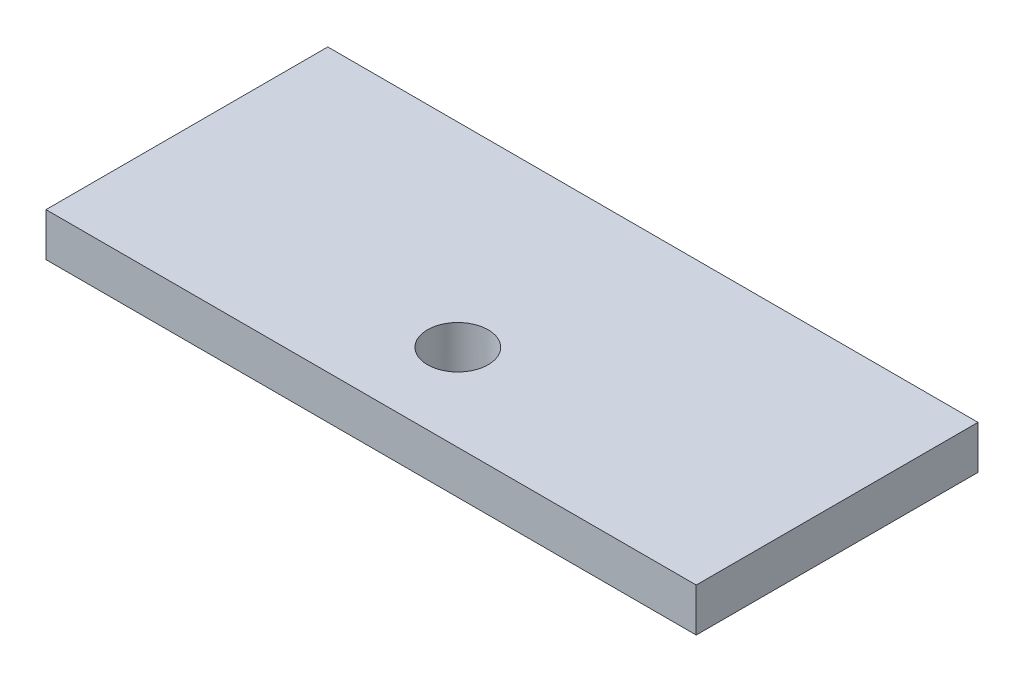
SolidWorks part; units mm, degrees
material "6061 Alloy"
ref_plane "Front Plane" through (0, 0, 0) normal (0, 0, 1) x (1, 0, 0)
ref_plane "Top Plane" through (0, 0, 0) normal (0, 1, 0) x (1, 0, 0)
ref_plane "Right Plane" through (0, 0, 0) normal (1, 0, 0) x (0, 0, -1)
sketch "Sketch1" plane through (0, 0, 0) normal (0, 1, 0) x (1, 0, 0)
  line L1 (-75, -32.5) -> (75, -32.5)
  line L2 (-75, -32.5) -> (-75, 32.5)
  line L3 (-75, 32.5) -> (75, 32.5)
  line L4 (75, -32.5) -> (75, 32.5)
  line L5 (-75, -32.5) -> (75, 32.5) construction
  line L6 (-75, 32.5) -> (75, -32.5) construction
  point P0 (0, 0)
  dimension "D1" = 150
  dimension "D2" = 65
extrude "Boss-Extrude1" add sketch "Sketch1" along normal blind 10
sketch "Sketch2" plane through (0, 0, 0) normal (0, 1, 0) x (1, 0, 0)
  line L0 (0, 0) -> (0, -46.7949) construction
  line L1 (-75, -32.5) -> (75, -32.5) construction
  circle A0 centre (0, -12.5) radius 7
  dimension "D1" = 14
  dimension "D2" = 20
extrude "Cut-Extrude2" cut sketch "Sketch2" against normal through all and the other way through all
